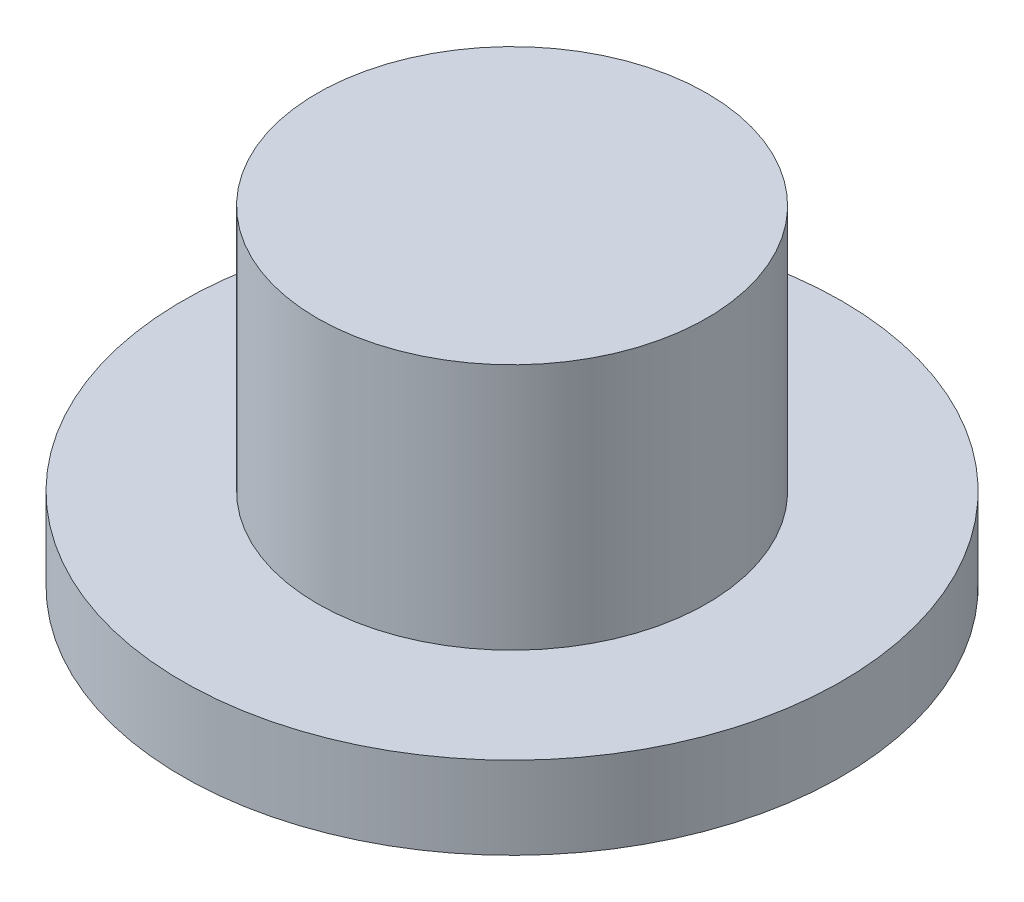
SolidWorks part; units mm, degrees
ref_plane "Alzado" through (0, 0, 0) normal (0, 0, 1) x (1, 0, 0)
ref_plane "Planta" through (0, 0, 0) normal (0, 1, 0) x (1, 0, 0)
ref_plane "Vista lateral" through (0, 0, 0) normal (1, 0, 0) x (0, 0, -1)
sketch "Croquis1" plane through (0, 0, 0) normal (0, 1, 0) x (1, 0, 0)
  circle A0 centre (0, 0) radius 2.365
  dimension "D1" = 4.73
extrude "Saliente-Extruir1" add sketch "Croquis1" along normal blind 3
sketch "Croquis2" plane through (0, 0, 0) normal (0, -1, 0) x (1, 0, 0)
  circle A0 centre (0, 0) radius 4
  dimension "D1" = 8
extrude "Saliente-Extruir2" add sketch "Croquis2" along normal blind 1
